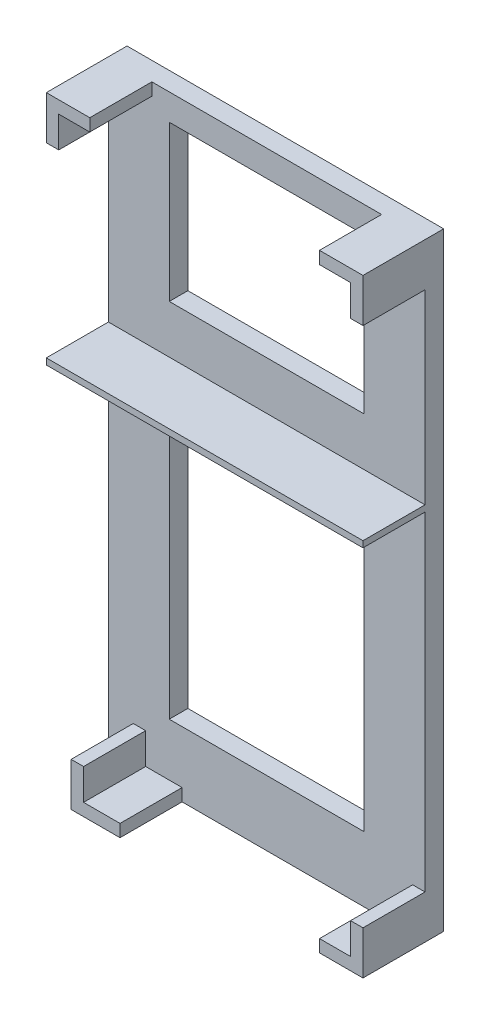
SolidWorks part; units mm, degrees
material "ABS"
ref_plane "Front Plane" through (0, 0, 0) normal (0, 0, 1) x (1, 0, 0)
ref_plane "Top Plane" through (0, 0, 0) normal (0, 1, 0) x (1, 0, 0)
ref_plane "Right Plane" through (0, 0, 0) normal (1, 0, 0) x (0, 0, -1)
sketch "Sketch1" plane through (0, 0, 0) normal (0, 0, 1) x (1, 0, 0)
  line L0 (25.5, 98) -> (25.5, 61) construction
  line L1 (0, 0) -> (51, 0)
  line L2 (0, 0) -> (0, 98)
  line L3 (0, 98) -> (51, 98)
  line L4 (51, 0) -> (51, 98)
  line L5 (0, 61) -> (51, 61)
  line L6 (51, 61) -> (51, 60)
  line L7 (51, 60) -> (0, 60)
  line L8 (0, 60) -> (0, 61)
  line L9 (51, 61) -> (51, 60)
  line L10 (0, 60) -> (0, 61)
  line L11 (51, 60) -> (51, 61)
  line L12 (25.5, 60) -> (25.5, 0) construction
  dimension "D1" = 98
  dimension "D2" = 51
  dimension "D3" = 37
  dimension "D4" = 60
extrude "Boss-Extrude2" add sketch "Sketch1" along normal blind 3 contours L2 L1 L4 L3
sketch "Sketch3" plane through (0, 0, 3) normal (0, 0, 1) x (1, 0, 0)
  line L0 (0, 98) -> (7, 98)
  line L1 (0, 98) -> (51, 98) construction
  line L2 (7, 98) -> (7, 96)
  line L3 (7, 96) -> (2, 96)
  line L4 (2, 96) -> (2, 91)
  line L5 (2, 91) -> (0, 91)
  line L6 (0, 0) -> (0, 98) construction
  line L7 (0, 91) -> (0, 98)
  line L8 (51, 98) -> (44, 98)
  line L9 (44, 98) -> (44, 96)
  line L10 (44, 96) -> (49, 96)
  line L11 (49, 96) -> (49, 91)
  line L12 (49, 91) -> (51, 91)
  line L13 (51, 0) -> (51, 98) construction
  line L14 (51, 91) -> (51, 98)
  line L16 (0, 0) -> (51, 0) construction
  line L22 (51, 0) -> (44, 0)
  line L23 (44, 0) -> (44, 2)
  line L24 (44, 2) -> (49, 2)
  line L25 (49, 2) -> (49, 7)
  line L26 (49, 7) -> (51, 7)
  line L27 (51, 7) -> (51, 0)
  dimension "D1" = 2
  dimension "D2" = 2
  dimension "D3" = 5
  dimension "D4" = 5
  dimension "D5" = 2
  dimension "D6" = 2
  dimension "D7" = 5
  dimension "D8" = 5
  dimension "D13" = 2
  dimension "D14" = 2
  dimension "D15" = 5
  dimension "D16" = 5
extrude "Boss-Extrude3" add sketch "Sketch3" along normal blind 10
sketch "Sketch4" plane through (0, 0, 3) normal (0, 0, 1) x (1, 0, 0)
  line L0 (4, 0) -> (4, 7)
  line L1 (0, 0) -> (51, 0) construction
  line L2 (4, 7) -> (6, 7)
  line L3 (6, 7) -> (6, 2)
  line L4 (6, 2) -> (11.8695, 2)
  line L5 (11.8695, 2) -> (11.8695, 0)
  line L6 (11.8695, 0) -> (4, 0)
  line L7 (0, 0) -> (0, 98) construction
  dimension "D1" = 5
  dimension "D2" = 2
  dimension "D3" = 2
  dimension "D4" = 4
extrude "Boss-Extrude4" add sketch "Sketch4" along normal blind 10 contours L6 L0 L2 L3 L4 L5
sketch "Sketch5" plane through (0, 0, 3) normal (0, 0, 1) x (1, 0, 0)
  line L0 (0, 61) -> (51, 61)
  line L1 (51, 61) -> (51, 60)
  line L2 (51, 60) -> (0, 60)
  line L3 (0, 60) -> (0, 61)
extrude "Boss-Extrude5" add sketch "Sketch5" along normal blind 10 contours L3 L0 L1 L2
sketch "Sketch6" plane through (0, 0, 3) normal (0, 0, 1) x (1, 0, 0)
  line L0 (39.8, 93.7705) -> (9.8, 93.7705)
  line L1 (9.8, 93.7705) -> (9.8, 68.7705)
  line L2 (9.8, 68.7705) -> (41.2, 68.7705)
  line L3 (41.2, 68.7705) -> (41.2, 93.7705)
  line L4 (41.2, 93.7705) -> (39.8, 93.7705)
  line L5 (0, 0) -> (0, 98) construction
  line L7 (51, 0) -> (51, 98) construction
  line L9 (0, 0) -> (51, 0) construction
  line L10 (39.8, 50.5) -> (9.8, 50.5)
  line L11 (9.8, 50.5) -> (9.8, 10.5)
  line L12 (9.8, 10.5) -> (41.2, 10.5)
  line L13 (41.2, 10.5) -> (41.2, 50.5)
  line L14 (41.2, 50.5) -> (39.8, 50.5)
  line L15 (51, 60) -> (0, 60) construction
  dimension "D1" = 25
  dimension "D2" = 30
  dimension "D3" = 9.8
  dimension "D4" = 9.8
  dimension "D5" = 40
  dimension "D6" = 30
  dimension "D7" = 10.5
  dimension "D8" = 9.5
extrude "Cut-Extrude1" cut sketch "Sketch6" against normal blind 10 contours L4 L0 L1 L2 L3 | L10 L11 L12 L13 L14
